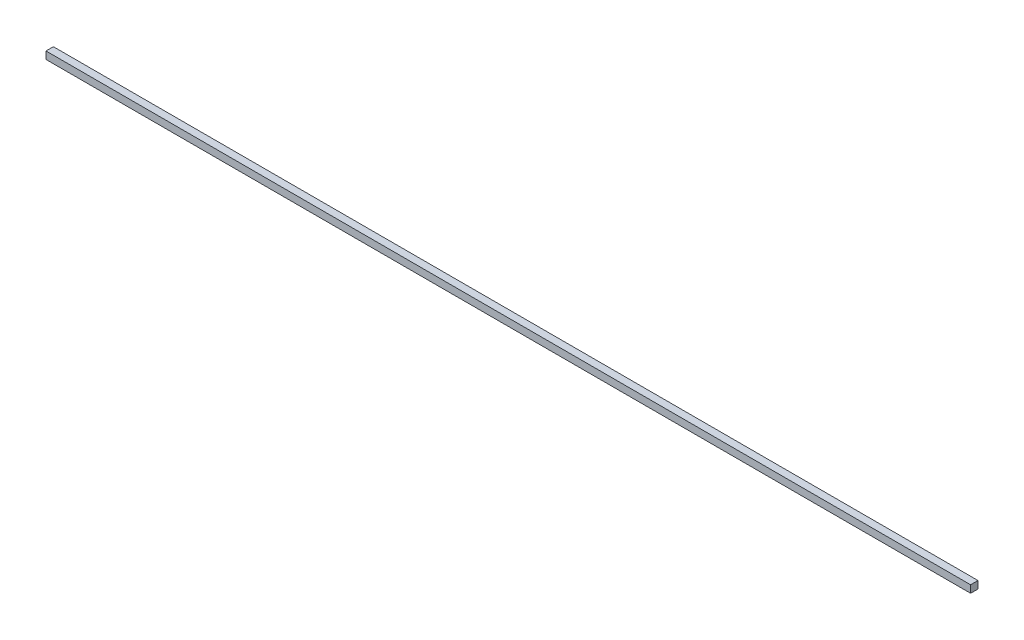
SolidWorks part; units mm, degrees
ref_plane "Front Plane" through (0, 0, 0) normal (0, 0, 1) x (1, 0, 0)
ref_plane "Top Plane" through (0, 0, 0) normal (0, 1, 0) x (1, 0, 0)
ref_plane "Right Plane" through (0, 0, 0) normal (1, 0, 0) x (0, 0, -1)
sketch "Sketch1" plane through (0, 0, 0) normal (0, 1, 0) x (1, 0, 0)
  line L0 (-625, 5) -> (625, -5) construction
  line L1 (-625, 5) -> (625, 5)
  line L2 (-625, 5) -> (-625, -5)
  line L3 (-625, -5) -> (625, -5)
  line L4 (625, 5) -> (625, -5)
  dimension "D1" = 1250
  dimension "D2" = 10
extrude "Boss-Extrude1" add sketch "Sketch1" along normal blind 10
